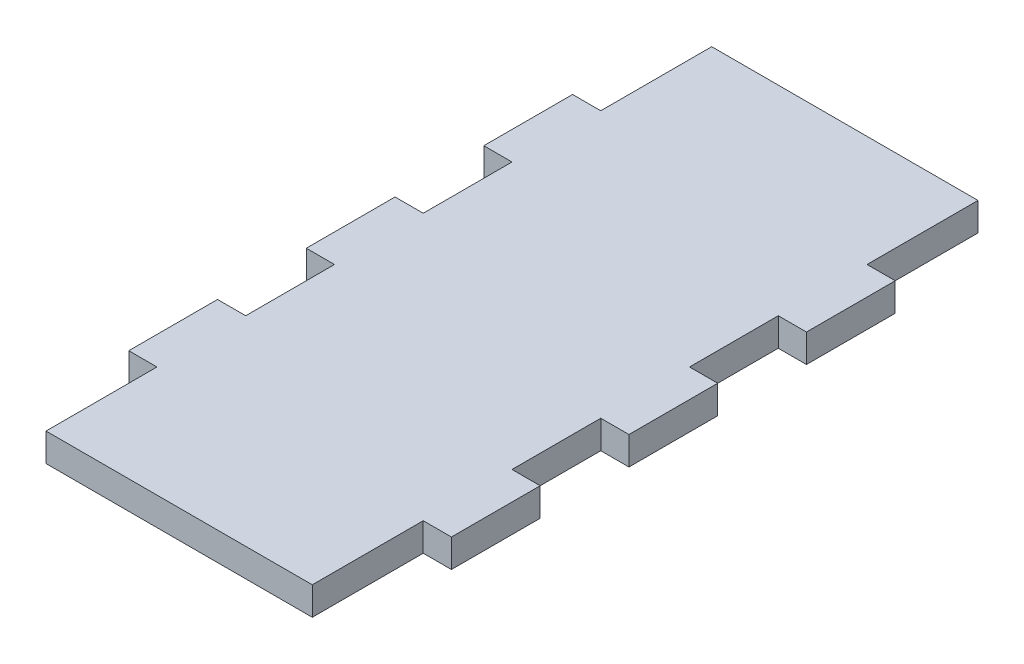
SolidWorks part; units mm, degrees
ref_plane "Front Plane" through (0, 0, 0) normal (0, 0, 1) x (1, 0, 0)
ref_plane "Top Plane" through (0, 0, 0) normal (0, 1, 0) x (1, 0, 0)
ref_plane "Right Plane" through (0, 0, 0) normal (1, 0, 0) x (0, 0, -1)
sketch "Sketch1" plane through (0, 0, 0) normal (0, 1, 0) x (1, 0, 0)
  line L1 (-15, -37.5) -> (15, -37.5)
  line L2 (-15, -37.5) -> (-15, 37.5)
  line L3 (-15, 37.5) -> (15, 37.5)
  line L4 (15, -37.5) -> (15, 37.5)
  line L5 (-15, -37.5) -> (15, 37.5) construction
  line L6 (-15, 37.5) -> (15, -37.5) construction
  point P0 (0, 0)
  point P6 (15, 14.916)
  dimension "D1" = 30
  dimension "D2" = 75
extrude "Boss-Extrude1" add sketch "Sketch1" along normal blind 3.175
sketch "Sketch2" plane through (0, 3.175, 0) normal (0, 1, 0) x (1, 0, 0)
  line L0 (-15, 0) -> (15, 0) construction
  line L1 (-15, 37.5) -> (-15, -37.5) construction
  line L2 (15, -37.5) -> (15, 37.5) construction
  line L3 (0, 0) -> (0, 37.5) construction
  line L4 (15, 37.5) -> (-15, 37.5) construction
  line L5 (-15, -5) -> (-15, 5)
  line L14 (-15, -25) -> (-18.175, -25)
  line L15 (-15, -25) -> (-15, -15)
  line L16 (-15, -15) -> (-18.175, -15)
  line L17 (-18.175, -25) -> (-18.175, -15)
  line L18 (-15, -5) -> (-18.175, -5)
  line L19 (-18.175, -5) -> (-18.175, 5)
  line L20 (-15, 5) -> (-18.175, 5)
  line L21 (-15, 15) -> (-15, 25)
  line L22 (-15, 15) -> (-18.175, 15)
  line L23 (-18.175, 15) -> (-18.175, 25)
  line L24 (-15, 25) -> (-18.175, 25)
  line L25 (-18.175, 0) -> (-15, 0) construction
  line L26 (15, -15) -> (18.175, -15)
  line L27 (18.175, -25) -> (18.175, -15)
  line L28 (15, -25) -> (18.175, -25)
  line L29 (15, -25) -> (15, -15)
  line L30 (15, -5) -> (18.175, -5)
  line L31 (18.175, -5) -> (18.175, 5)
  line L32 (15, 5) -> (18.175, 5)
  line L33 (15, -5) -> (15, 5)
  line L34 (15, 15) -> (18.175, 15)
  line L35 (18.175, 15) -> (18.175, 25)
  line L36 (15, 25) -> (18.175, 25)
  line L37 (15, 15) -> (15, 25)
  dimension "D1" = 3.175
  dimension "D2" = 10
  dimension "D4" = 10
  dimension "D3" = 3
extrude "Boss-Extrude2" add sketch "Sketch2" against normal up to surface (3.175 mm away) up to face at (0, 0, 0)
